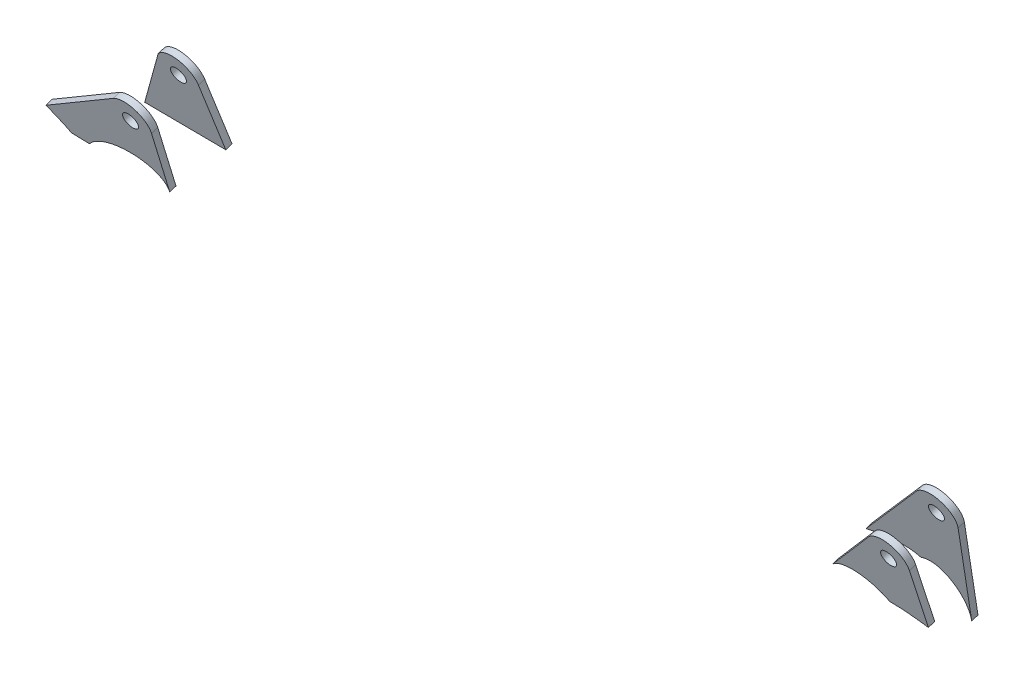
SolidWorks part; units mm, degrees
material "1.0545 (S355N)"
ref_plane "Płaszczyzna XY" through (0, 0, 0) normal (0, 0, 1) x (1, 0, 0)
ref_plane "Płaszczyzna XZ" through (0, 0, 0) normal (0, 1, 0) x (1, 0, 0)
ref_plane "Płaszczyzna YZ" through (0, 0, 0) normal (1, 0, 0) x (0, 0, -1)
ref_plane "Płaszczyzna1" through (0, -49.0079, 148.909) normal (0, 0.3126, -0.9499) x (-1, 0, 0)
ref_plane "Płaszczyzna2" through (0, -45.8818, 139.4102) normal (0, 0.3126, -0.9499) x (-1, 0, 0)
sketch "Szkic1" plane through (0, -45.8818, 139.4102) normal (0, 0.3126, -0.9499) x (-1, 0, 0)
  line L0 (-1507.3247, 391.926) -> (-1497.0477, 339.1763)
  line L1 (-1490.8329, 399.9784) -> (-1454.8598, 358.6318)
  line L2 (-1161.454, 394.6763) -> (-1164.4504, 364.332)
  line L4 (-1127.579, 364.7903) -> (-1144.6549, 399.7676)
  circle A0 centre (-1152, 393.7427) radius 3.5
  circle A1 centre (-1498, 393.7427) radius 3.5
  arc A2 (-1144.6549, 399.7676) -> (-1161.454, 394.6763) centre (-1152, 393.7427) ccw
  arc A3 (-1490.8329, 399.9784) -> (-1507.3247, 391.926) centre (-1498, 393.7427) ccw
  spline S1 degree 3 poles (-1164.4504, 364.332) (-1152.6111, 364.4926) (-1140.3128, 364.6453) (-1127.579, 364.7903) knots 0.951483 0.951483 0.951483 0.951483 1 1 1 1 weights 0.978495 0.985298 0.992466 1
  spline S11 degree 3 poles (-1497.0477, 339.1763) (-1500.2959, 355.8487) (-1491.0713, 366.1445) (-1480.5742, 360.5027) knots 0.56226 0.56226 0.56226 0.56226 1 1 1 1 weights 0.855161 0.563995 0.612275 1
  spline S13 degree 3 poles (-1480.5742, 360.5027) (-1475.882, 362.9501) (-1466.8646, 362.76) (-1454.8598, 358.6318) knots 0.566885 0.566885 0.566885 0.566885 0.725492 0.725492 0.725492 0.725492 weights 0.768249 0.613352 0.525537 0.504805
  dimension "D1" = 7
  dimension "D2" = 6
  dimension "D4" = 6
  dimension "D3" = 30
extrude "Dodanie-wyciągnięcie1" add sketch "Szkic1" along normal blind 3
ref_plane "Płaszczyzna3" through (0, -53.072, 161.2574) normal (0, 0.3126, -0.9499) x (-1, 0, 0)
sketch "Szkic2" plane through (0, -53.072, 161.2574) normal (0, 0.3126, -0.9499) x (-1, 0, 0)
  line L0 (-1146.4645, 401.4634) -> (-1106.9885, 373.1601)
  line L2 (-1161.4948, 393.4289) -> (-1160.5113, 363.6713)
  line L3 (-1490.8183, 399.9615) -> (-1464.756, 369.8638)
  line L4 (-1507.4997, 393.6666) -> (-1507.2719, 365.2481)
  line L6 (-1124.3083, 364.8679) -> (-1116.2153, 365.1354)
  circle A1 centre (-1152, 393.7427) radius 3.5
  circle A3 centre (-1498, 393.7427) radius 3.5
  arc A4 (-1146.4645, 401.4634) -> (-1161.4948, 393.4289) centre (-1152, 393.7427) ccw
  arc A5 (-1490.8183, 399.9615) -> (-1507.4997, 393.6666) centre (-1498, 393.7427) ccw
  circle A8 centre (-1152, 393.7427) radius 3.5 construction
  circle A9 centre (-1498, 393.7427) radius 3.5 construction
  spline S1 degree 3 poles (-1507.2719, 365.2481) (-1501.1128, 366.7295) (-1495.3335, 367.4673) (-1490.2884, 367.5377) knots 0.829977 0.829977 0.829977 0.829977 0.944346 0.944346 0.944346 0.944346 weights 0.725471 0.755309 0.806483 0.878992
  spline S3 degree 3 poles (-1490.2884, 367.5377) (-1482.9246, 375.6892) (-1471.1606, 377.2601) (-1464.756, 369.8638) knots 0 0 0 0 0.854313 0.854313 0.854313 0.854313 weights 1 0.699634 0.655875 0.868722
  spline S7 degree 3 poles (-1160.5113, 363.6713) (-1160.5382, 364.486) (-1160.4465, 365.2591) (-1160.2561, 365.9858) (-1157.2256, 377.5486) (-1137.0297, 380.9126) (-1124.3083, 364.8679) knots 0.957483 0.957483 0.957483 0.957483 1 1 1 1.366617 1.366617 1.366617 1.366617 weights 0.844393 0.891441 0.94331 1 0.511178 0.380776 0.608796
  spline S9 degree 3 poles (-1116.2153, 365.1354) (-1114.2942, 367.2704) (-1111.2619, 369.9365) (-1106.9885, 373.1601) knots 0.553642 0.553642 0.553642 0.553642 0.604482 0.604482 0.604482 0.604482 weights 0.815244 0.76389 0.719184 0.681126
  dimension "D2" = 7
  dimension "D3" = 7
  dimension "D1" = 6
  dimension "D4" = 6
extrude "Dodanie-wyciągnięcie2" add sketch "Szkic2" along normal blind 3 separate body
